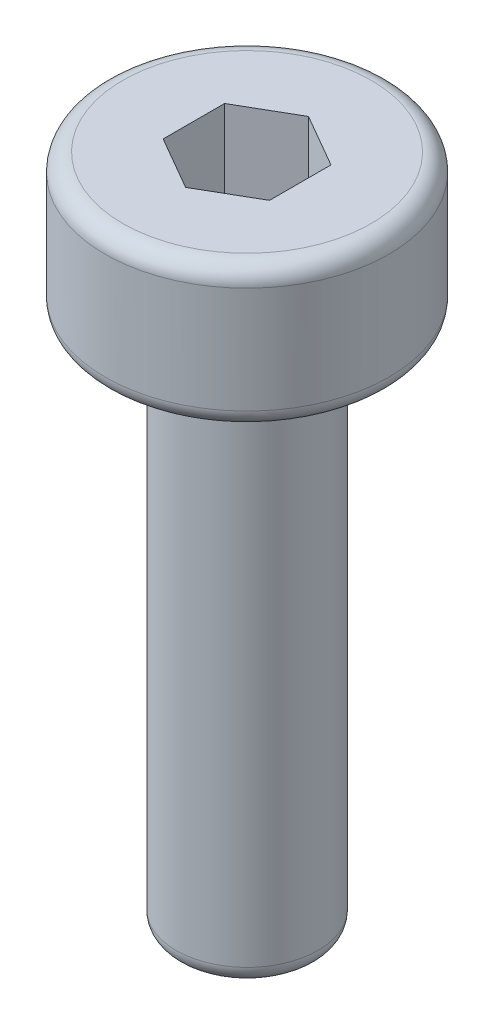
SolidWorks part; units mm, degrees
material "AISI 1020"
ref_plane "Plano frontal" through (0, 0, 0) normal (0, 0, 1) x (1, 0, 0)
ref_plane "Plano superior" through (0, 0, 0) normal (0, 1, 0) x (1, 0, 0)
ref_plane "Plano direito" through (0, 0, 0) normal (1, 0, 0) x (0, 0, -1)
sketch "Esboço1" plane through (0, 0, 0) normal (0, 0, 1) x (1, 0, 0)
  line L0 (0, -9.5) -> (0, 9.5)
  line L1 (0, 9.5) -> (-4, 9.5)
  line L2 (-4, 9.5) -> (-4, 5.5)
  line L3 (-4, 5.5) -> (-2, 5.5)
  line L4 (-2, 5.5) -> (-2, -9.5)
  line L5 (-2, -9.5) -> (0, -9.5)
  dimension "D1" = 2
  dimension "D2" = 4
  dimension "D3" = 4
  dimension "D4" = 15
revolve "Revolução1" add sketch "Esboço1" angle 360 about L0
sketch "Esboço2" plane through (0, 9.5, 0) normal (0, 1, 0) x (1, 0, 0)
  line L1 (1.5, -0.866) -> (1.5, 0.866)
  line L2 (1.5, 0.866) -> (0, 1.7321)
  line L3 (0, 1.7321) -> (-1.5, 0.866)
  line L4 (-1.5, 0.866) -> (-1.5, -0.866)
  line L5 (-1.5, -0.866) -> (0, -1.7321)
  line L6 (0, -1.7321) -> (1.5, -0.866)
  circle A0 centre (0, 0) radius 1.5 construction
  dimension "D1" = 3
extrude "Corte-extrusão1" cut sketch "Esboço2" against normal blind 6
fillet "Filete1" radius 0.5 10 edges at (-0.75, 3.5, 1.299) (-1.5, 3.5, 0) (-0.75, 3.5, -1.299) (0.75, 3.5, -1.299) (1.5, 3.5, 0) (0.75, 3.5, 1.299) (0, -9.5, -2) (0, 5.5, -2) (0, 5.5, -4) (0, 9.5, -4)
